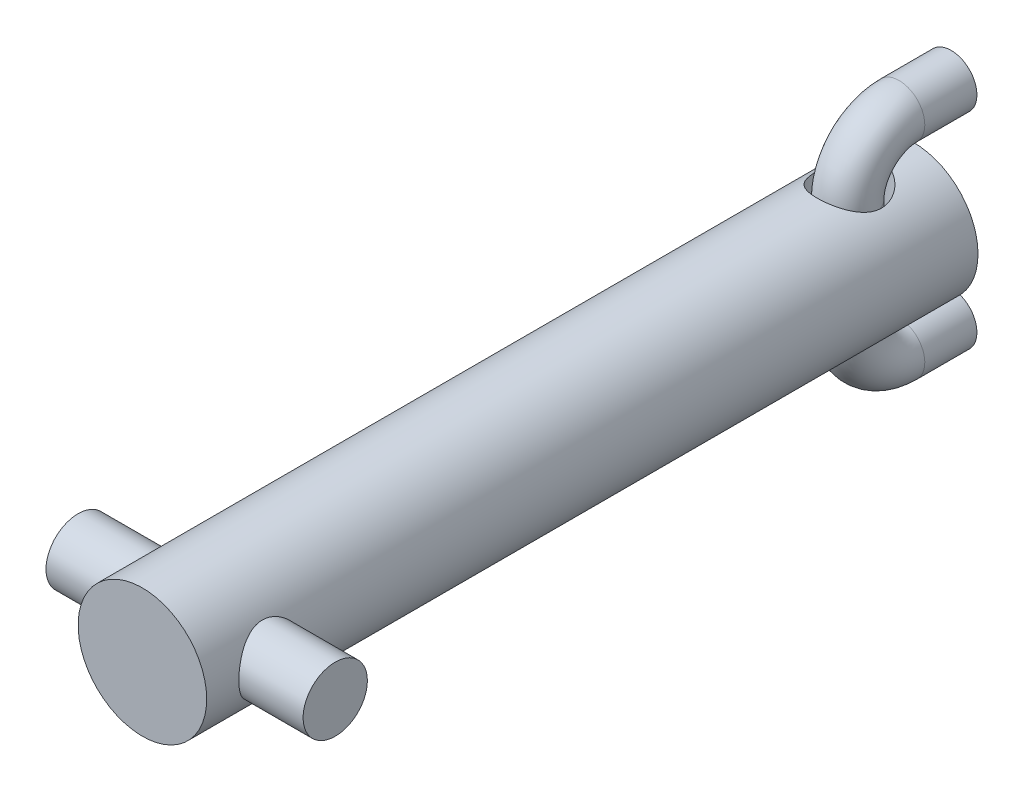
SolidWorks part; units mm, degrees
material "Cast Carbon Steel"
ref_plane "Front Plane" through (0, 0, 0) normal (0, 0, 1) x (1, 0, 0)
ref_plane "Top Plane" through (0, 0, 0) normal (0, 1, 0) x (1, 0, 0)
ref_plane "Right Plane" through (0, 0, 0) normal (1, 0, 0) x (0, 0, -1)
sketch "Sketch1" plane through (0, 0, 0) normal (0, 0, 1) x (1, 0, 0)
  circle A0 centre (0, 0) radius 3.175
  dimension "D1" = 6.35
extrude "Boss-Extrude1" add sketch "Sketch1" along normal blind 38.1
sketch "Sketch2" plane through (0, 0, 0) normal (0, 1, 0) x (1, 0, 0)
  circle A0 centre (0, -3.175) radius 1.5875
  dimension "D2" = 3.175
  dimension "D1" = 3.175
extrude "Cut-Extrude1" cut sketch "Sketch2" against normal mid plane 31.75
sketch "Sketch3" plane through (0, 0, 0) normal (1, 0, 0) x (0, 0, -1)
  line L0 (-38.1, 3.175) -> (-38.1, -3.175) construction
  circle A0 centre (-34.925, 0) radius 1.5875
  dimension "D1" = 3.175
  dimension "D2" = 3.175
  dimension "D3" = 3.175
extrude "Boss-Extrude2" add sketch "Sketch3" along normal mid plane 12.7
sketch "Sketch4" plane through (0, 0, 0) normal (1, 0, 0) x (0, 0, -1)
  line L0 (-3.263, -2.6975) -> (-3.263, 2.3825)
  line L1 (-0.723, 4.9225) -> (1.8504, 4.9225)
  line L2 (-0.723, -5.2375) -> (1.8504, -5.2375)
  arc A0 (-3.263, -2.6975) -> (-0.723, -5.2375) centre (-0.723, -2.6975) ccw
  arc A1 (-0.723, 4.9225) -> (-3.263, 2.3825) centre (-0.723, 2.3825) ccw
  point P3 (-3.263, -0.1575)
  point P7 (-3.263, -5.2375)
  point P10 (-3.263, 4.9225)
  dimension "D2" = 2.54
  dimension "D1" = 10.16
  dimension "D3" = 1.8504
  dimension "D4" = 3.263
  dimension "D5" = 4.9225
sweep "Sweep1" add path "Sketch4" circular profile diameter 2.54 parameters "D3"=2.54
